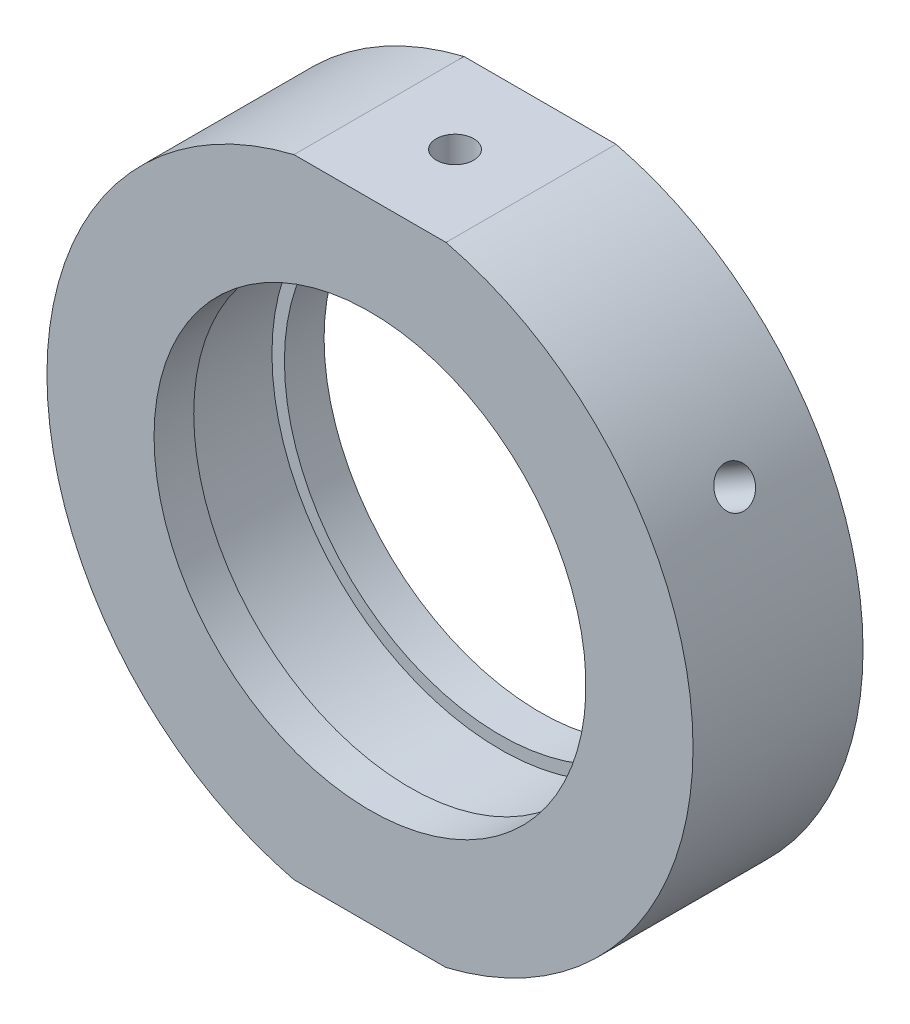
SolidWorks part; units mm, degrees
ref_plane "前视基准面" through (0, 0, 0) normal (0, 0, 1) x (1, 0, 0)
ref_plane "上视基准面" through (0, 0, 0) normal (0, 1, 0) x (1, 0, 0)
ref_plane "右视基准面" through (0, 0, 0) normal (1, 0, 0) x (0, 0, -1)
sketch "草图1" plane through (0, 0, 0) normal (0, 1, 0) x (1, 0, 0)
  line L0 (0, 31.9391) -> (0, -26.491) construction
  line L1 (28.5, 7.5) -> (28.5, -7.5)
  line L6 (28.5, -7.5) -> (19.05, -7.5)
  line L7 (19.05, -7.5) -> (19.05, -4)
  line L8 (19.05, -4) -> (20.15, -4)
  line L9 (20.15, -4) -> (20.15, 4)
  line L10 (20.15, 4) -> (19.05, 4)
  line L11 (19.05, 4) -> (19.05, 7.5)
  line L12 (19.05, 7.5) -> (28.5, 7.5)
  line L17 (19.05, 0) -> (-5.0345, 0) construction
  point P6 (20.15, 0)
  dimension "D2" = 20.15
  dimension "D3" = 19.05
  dimension "D4" = 19.05
  dimension "D5" = 15
  dimension "D6" = 3.5
  dimension "D7" = 7.5
  dimension "D9" = 28.5
  dimension "D14" = 8
  dimension "D15" = 4
  dimension "D18" = 0
revolve "旋转1" add sketch "草图1" angle 360 about L0
sketch "草图2" plane through (0, 0, 7.5) normal (0, 0, 1) x (1, 0, 0)
  line L0 (0, 0) -> (43.1523, 0) construction
  line L1 (-33.152, 36.9489) -> (30.8698, 36.9489)
  line L2 (-33.152, 36.9489) -> (-33.152, 27.7)
  line L3 (-33.152, 27.7) -> (30.8698, 27.7)
  line L4 (30.8698, 36.9489) -> (30.8698, 27.7)
  line L5 (30.8698, -36.9489) -> (30.8698, -27.7)
  line L6 (-33.152, -27.7) -> (30.8698, -27.7)
  line L7 (-33.152, -36.9489) -> (-33.152, -27.7)
  line L8 (-33.152, -36.9489) -> (30.8698, -36.9489)
  dimension "D1" = 27.7
extrude "切除-拉伸1" cut sketch "草图2" against normal blind 49
sketch "草图10" plane through (0, 0, 0) normal (0, 0, 1) x (1, 0, 0)
  line L0 (0, 27.7) -> (0, -27.7)
  line L1 (-6.7052, 27.7) -> (6.7052, 27.7) construction
  line L2 (-6.7052, -27.7) -> (6.7052, -27.7) construction
  line L3 (0, 0) -> (-24.6817, 14.25)
  line L4 (0, 0) -> (24.6817, 14.25)
  arc A2 (6.7052, -27.7) -> (6.7052, 27.7) centre (0, 0) ccw construction
  arc A3 (-6.7052, 27.7) -> (-6.7052, -27.7) centre (0, 0) ccw construction
  arc A4 (24.6817, 14.25) -> (6.7052, 27.7) centre (0, 0) ccw
  arc A5 (-6.7052, 27.7) -> (-24.6817, 14.25) centre (0, 0) ccw
  dimension "D1" = 60
  dimension "D2" = 60
hole_wizard "M4 螺纹孔2" positions "草图15" profile "草图16" tap size "M4" standard "ISO"
sketch "草图15" plane through (0, 27.7, 0) normal (0, 1, 0) x (1, 0, 0)
  point P0 (0, 0)
sketch "草图16" plane through (0, 27.7, 0) normal (1, 0, 0) x (0, 0, 1)
  line L0 (0, 0) -> (0, 6.4914)
  line L1 (0, 6.4914) -> (1.65, 5.5)
  line L2 (1.65, 5.5) -> (1.65, 0)
  line L5 (1.65, 0) -> (0, 0)
  line L10 (0, 6.4914) -> (-1.65, 5.5) construction
  line L11 (0, -6.35) -> (0, 107.95) construction
  dimension "螺纹孔钻头直径" = 3.3
  dimension "螺纹孔钻头深度" = 5.5
  dimension "导头角度" = 118
cosmetic thread "孔螺蚊线1" parameters "D1"=5.5, "D2"=4
hole_wizard "M6 螺纹孔2" positions "草图17" profile "草图18" tap size "M6" standard "ISO"
sketch "草图17" plane through (0, -27.7, 0) normal (0, -1, 0) x (-1, 0, 0)
  point P0 (0, 0)
sketch "草图18" plane through (0, -27.7, 0) normal (1, 0, 0) x (0, 0, -1)
  line L0 (0, 0) -> (0, 7.0022)
  line L1 (0, 7.0022) -> (2.5, 5.5)
  line L2 (2.5, 5.5) -> (2.5, 0)
  line L5 (2.5, 0) -> (0, 0)
  line L10 (0, 7.0022) -> (-2.5, 5.5) construction
  line L11 (0, -6.35) -> (0, 107.95) construction
  dimension "螺纹孔钻头直径" = 5
  dimension "螺纹孔钻头深度" = 5.5
  dimension "导头角度" = 118
cosmetic thread "孔螺蚊线2" parameters "D1"=5.5, "D2"=6
hole_wizard "M4 螺纹孔3" positions "3D草图4" profile "草图22" tap size "M4" standard "ISO"
sketch3d "3D草图4"
  point P0 (-24.6817, 14.25, 0)
  point P4 (24.6817, 14.25, 0)
  point P7 (24.6817, 14.25, 0)
  point P11 (-24.6817, 14.25, 0)
  point P15 (24.6817, 14.25, 0)
  point P17 (24.6817, 14.25, 0)
sketch "草图22" plane through (24.6817, 14.25, 0) normal (0, 0, 1) x (-0.5, 0.866, 0)
  line L0 (0, 0) -> (0, 14.3914)
  line L1 (0, 14.3914) -> (1.65, 13.4)
  line L2 (1.65, 13.4) -> (1.65, 0)
  line L5 (1.65, 0) -> (0, 0)
  line L10 (0, 14.3914) -> (-1.65, 13.4) construction
  line L11 (0, -6.35) -> (0, 107.95) construction
  dimension "螺纹孔钻头直径" = 3.3
  dimension "螺纹孔钻头深度" = 13.4
  dimension "导头角度" = 118
cosmetic thread "孔螺蚊线4" parameters "D1"=8.0514, "D2"=4
cosmetic thread "孔螺蚊线5" parameters "D1"=8.0514, "D2"=4
